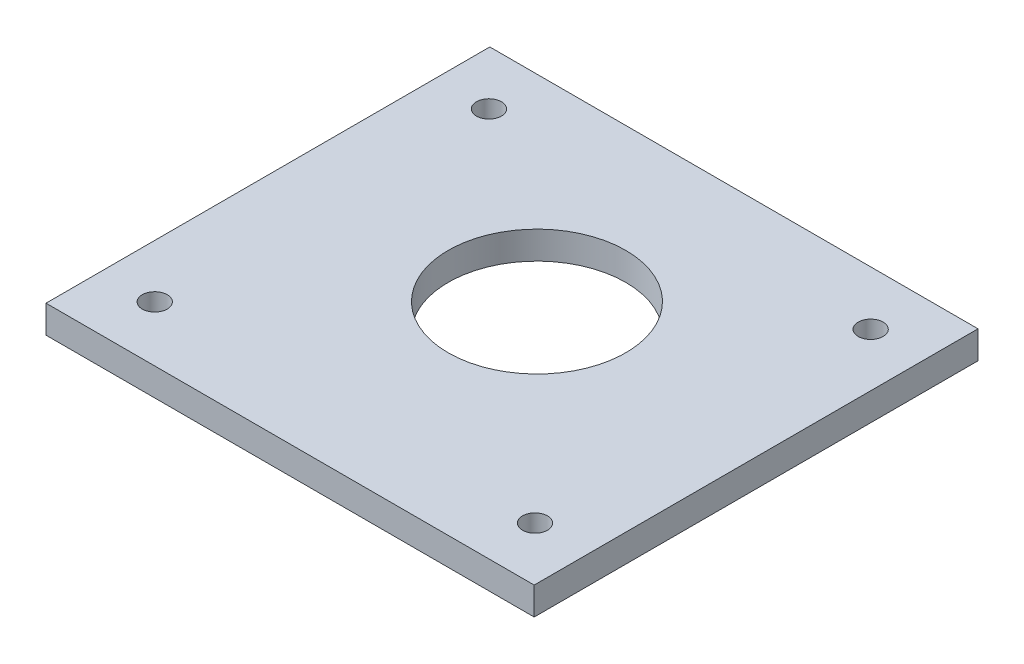
SolidWorks part; units mm, degrees
ref_plane "Спереди" through (0, 0, 0) normal (0, 0, 1) x (1, 0, 0)
ref_plane "Сверху" through (0, 0, 0) normal (0, 1, 0) x (1, 0, 0)
ref_plane "Справа" through (0, 0, 0) normal (1, 0, 0) x (0, 0, -1)
sketch "Эскиз1" plane through (0, 0, 0) normal (0, 1, 0) x (1, 0, 0)
  line L0 (-34.4, 45.4663) -> (-34.4, -37.5671) construction
  line L1 (-41.6086, 30.25) -> (64.5714, 30.25) construction
  line L2 (0, 66.5921) -> (0, -58.5092) construction
  line L3 (34.4, 45.4663) -> (34.4, -37.5671) construction
  line L4 (-93.5963, 0) -> (75.0424, 0) construction
  line L5 (-41.6086, -30.25) -> (64.5714, -30.25) construction
  line L7 (-44, 40) -> (44, 40)
  line L8 (-44, 40) -> (-44, -40)
  line L9 (-44, -40) -> (44, -40)
  line L10 (44, 40) -> (44, -40)
  line L11 (-44, 40) -> (44, -40) construction
  line L12 (-44, -40) -> (44, 40) construction
  circle A0 centre (-34.4, 30.25) radius 2.25
  circle A1 centre (34.4, 30.25) radius 2.25
  circle A2 centre (34.4, -30.25) radius 2.25
  circle A3 centre (-34.4, -30) radius 2.25
  circle A6 centre (0, 4.5) radius 16
  point P13 (0, 0)
  point P22 (33.6, 29.9973)
  point P23 (0, 0)
  dimension "D1" = 80
  dimension "D3" = 32
  dimension "D4" = 68.8
  dimension "D5" = 35.5
  dimension "D6" = 60.5
  dimension "D7" = 4.5
  dimension "D2" = 88
extrude "Бобышка-Вытянуть1" add sketch "Эскиз1" along normal blind 5
